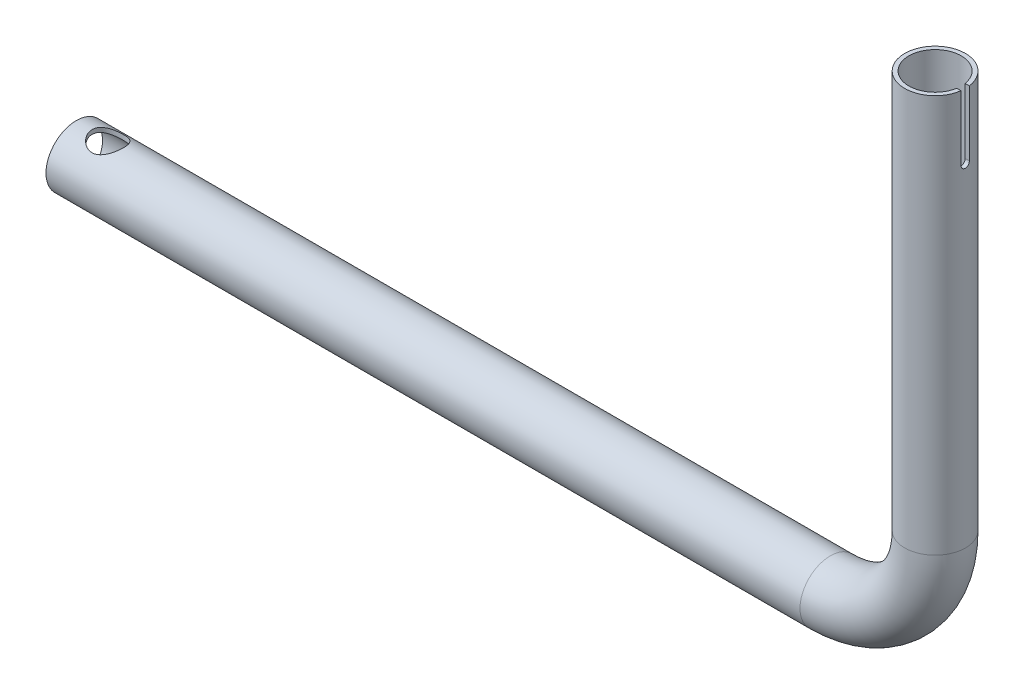
SolidWorks part; units mm, degrees
ref_plane "前基準面" through (0, 0, 0) normal (0, 0, 1) x (1, 0, 0)
ref_plane "上基準面" through (0, 0, 0) normal (0, 1, 0) x (1, 0, 0)
ref_plane "右基準面" through (0, 0, 0) normal (1, 0, 0) x (0, 0, -1)
sketch "草圖1" plane through (0, 0, 0) normal (0, 0, 1) x (1, 0, 0)
  line L0 (0, 0) -> (360, 0)
  line L1 (410, 50) -> (410, 240)
  arc A0 (410, 50) -> (360, 0) centre (360, 50) cw
  point P6 (410, 0)
  dimension "D3" = 50
  dimension "D1" = 240
  dimension "D2" = 410
ref_plane "平面1" through (410, 240, 0) normal (0, 1, 0) x (1, 0, 0)
sketch "草圖3" plane through (60, 240, 0) normal (0, 1, 0) x (1, 0, 0)
  line L0 (-60, 0) -> (300, 0) construction
  circle A0 centre (350, 0) radius 12.5
  dimension "D1" = 25
ref_plane "平面2" through (410, 236, 0) normal (0, 1, 0) x (1, 0, 0)
sweep "掃出5" add profiles "草圖3" path "草圖1"
shell "薄殼7" thickness 2
sketch "草圖10" plane through (0, 0, 0) normal (0, 1, 0) x (1, 0, 0)
  line L0 (2.6124, 0) -> (-38.3227, 0) construction
  line L1 (3.1449, 0) -> (-17.8551, 0) construction
  line L2 (-17.8551, -30.5) -> (-17.8551, 30.5) construction
  line L3 (-17.8551, 33.9853) -> (-17.8551, 41.5)
  line L4 (-17.8551, -33.9853) -> (-17.8551, -41.5)
  line L5 (-20.8551, -33.9853) -> (-20.8551, -41.5)
  line L6 (-20.8551, 33.9853) -> (-20.8551, 41.5)
  arc A0 (-16.1972, -31.3022) -> (-16.1972, 31.3022) centre (-31.8551, 0) ccw
  arc A1 (-17.8551, 33.9853) -> (-16.1972, 31.3022) centre (-14.8551, 33.9853) ccw
  arc A2 (-17.8551, -33.9853) -> (-16.1972, -31.3022) centre (-14.8551, -33.9853) cw
  arc A3 (-20.8551, -33.9853) -> (-17.5394, -28.6192) centre (-14.8551, -33.9853) cw
  arc A4 (-17.5394, -28.6192) -> (-17.5394, 28.6192) centre (-31.8551, 0) ccw
  arc A5 (-20.8551, 33.9853) -> (-17.5394, 28.6192) centre (-14.8551, 33.9853) ccw
  arc A6 (-20.8551, -41.5) -> (-17.8551, -41.5) centre (-19.3551, -41.5) ccw
  arc A7 (-20.8551, 41.5) -> (-17.8551, 41.5) centre (-19.3551, 41.5) cw
  arc A8 (-16.1972, -31.3022) -> (-16.1972, 31.3022) centre (-31.8551, 0) ccw construction
  dimension "D2" = 3
  dimension "D3" = 3
  dimension "D5" = 35
  dimension "D1" = 21
  dimension "D6" = 83
  dimension "D4" = 3
sketch "草圖12" [suppressed] plane through (0, 0, 0) normal (0, 1, 0) x (1, 0, 0)
  line L1 (-97.0175, 0.2332) -> (-57.7598, 0.2332) construction
  line L2 (-62.3637, -46.2583) -> (-62.3637, 46.8705) construction
  line L3 (-62.3637, -33.9853) -> (-62.3637, -41.5)
  line L4 (-62.3637, 33.9853) -> (-62.3637, 41.5)
  line L5 (-59.3637, 33.9853) -> (-59.3637, 41.5)
  line L6 (-59.3637, -33.9853) -> (-59.3637, -41.5)
  arc A0 (-64.0216, 31.3022) -> (-64.0216, -31.3022) centre (-48.3637, 0) ccw
  arc A1 (-62.3637, 33.9853) -> (-64.0216, 31.3022) centre (-65.3637, 33.9853) cw
  arc A2 (-64.0216, -31.3022) -> (-62.3637, -33.9853) centre (-65.3637, -33.9853) cw
  arc A3 (-59.3637, 33.9853) -> (-62.6795, 28.6192) centre (-65.3637, 33.9853) cw
  arc A4 (-62.6795, 28.6192) -> (-62.6795, -28.6192) centre (-48.3637, 0) ccw
  arc A5 (-62.6795, -28.6192) -> (-59.3637, -33.9853) centre (-65.3637, -33.9853) cw
  arc A6 (-59.3637, -41.5) -> (-62.3637, -41.5) centre (-60.8637, -41.5) cw
  arc A7 (-62.3637, 41.5) -> (-59.3637, 41.5) centre (-60.8637, 41.5) cw
  point P10 (-83.3637, 0)
  dimension "D1" = 70
  dimension "D2" = 21
  dimension "D4" = 3
  dimension "D3" = 83
  dimension "D5" = 3
extrude "填料-伸長4" [suppressed] add sketch "草圖12" along normal mid plane 40
sketch "草圖15" [suppressed] plane through (-62.3637, 0, 0) normal (-1, 0, 0) x (0, 0, 1)
  line L0 (37.7426, 20) -> (37.7426, -20) construction
  line L1 (33.9853, 20) -> (41.5, 20) construction
  line L2 (33.9853, -20) -> (41.5, -20) construction
  circle A0 centre (37.7426, 15) radius 2.6
  circle A1 centre (37.7426, -15) radius 2.6
  dimension "D1" = 5.2
  dimension "D2" = 5.2
  dimension "D3" = 5
  dimension "D4" = 5
extrude "除料-伸長3" [suppressed] cut sketch "草圖15" against normal up to next
mirror "鏡射2" [suppressed] about plane through (0, 0, 0) normal (0, 0, 1)
ref_plane "平面4" through (410, 0, 0) normal (1, 0, 0) x (0, 0, -1)
sketch "草圖18" plane through (410, 0, 0) normal (1, 0, 0) x (0, 0, -1)
  line L0 (-2, 240) -> (-2, 209)
  line L1 (12.5, 240) -> (-12.5, 240) construction
  line L3 (2, 209) -> (2, 240)
  line L4 (0, 240) -> (0, 191.7853) construction
  line L5 (14.5, 240) -> (-14.5, 240) construction
  arc A0 (-2, 209) -> (2, 209) centre (0, 209) ccw
  dimension "D3" = 4
  dimension "D2" = 33
  dimension "D1" = 4
extrude "除料-伸長4" cut sketch "草圖18" along normal through all
sketch "草圖19" plane through (0, 0, 0) normal (0, 1, 0) x (1, 0, 0)
  circle A0 centre (15, 0) radius 7.5
  dimension "D1" = 15
  dimension "D2" = 15
extrude "除料-伸長5" cut sketch "草圖19" against normal mid plane 50
